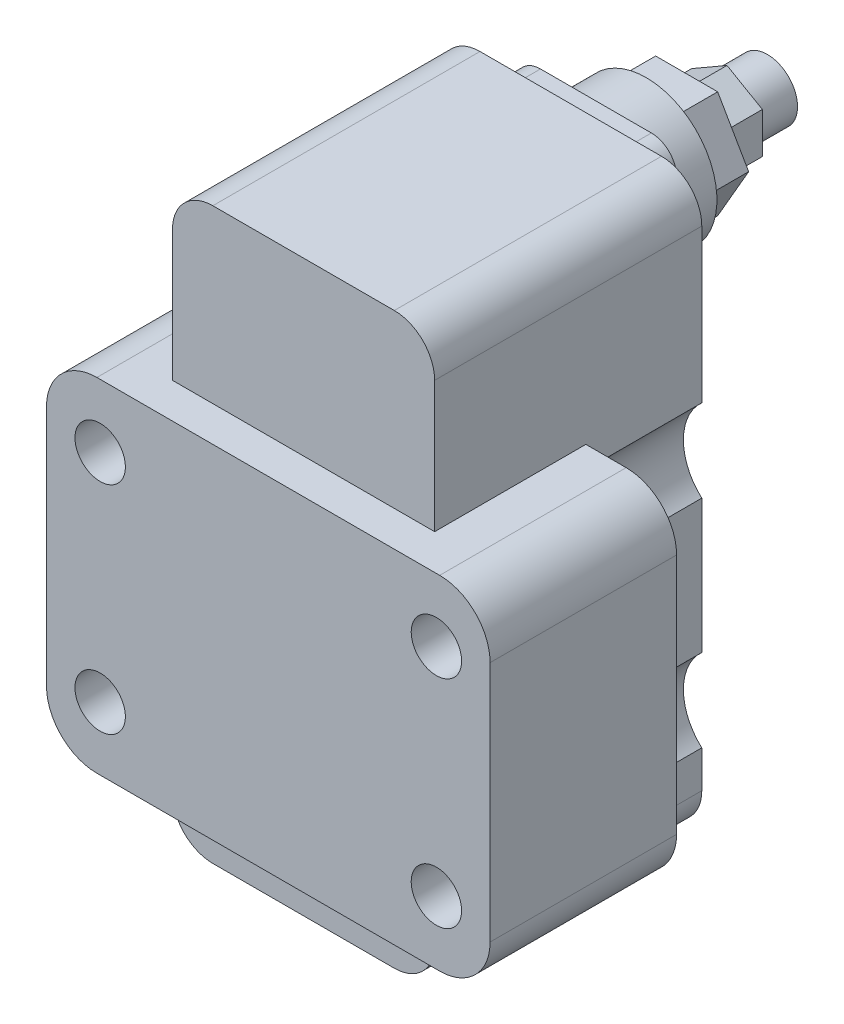
SolidWorks part; units mm, degrees
ref_plane "Front" through (0, 0, 0) normal (0, 0, 1) x (1, 0, 0)
ref_plane "Top" through (0, 0, 0) normal (0, 1, 0) x (1, 0, 0)
ref_plane "Right" through (0, 0, 0) normal (1, 0, 0) x (0, 0, -1)
sketch "草图1" plane through (0, 0, 0) normal (0, 0, 1) x (1, 0, 0)
  line L1 (-44, 34) -> (44, 34)
  line L2 (-44, 34) -> (-44, -34)
  line L3 (-44, -34) -> (44, -34)
  line L4 (44, 34) -> (44, -34)
  line L5 (-44, 34) -> (44, -34) construction
  line L6 (-44, -34) -> (44, 34) construction
  point P0 (0, 0)
  dimension "D1" = 68
  dimension "D2" = 88
extrude "凸台-拉伸1" add sketch "草图1" along normal blind 37
sketch "草图2" plane through (0, 0, 37) normal (0, 0, 1) x (1, 0, 0)
  line L1 (-44, -34) -> (44, -34) construction
  line L2 (-33.35, 21.45) -> (33.35, 21.45) construction
  line L3 (-33.35, 21.45) -> (-33.35, -21.45) construction
  line L4 (-33.35, -21.45) -> (33.35, -21.45) construction
  line L5 (33.35, 21.45) -> (33.35, -21.45) construction
  line L6 (-26, 68) -> (26, 68)
  line L7 (-26, 68) -> (-26, -45)
  line L8 (-26, -45) -> (26, -45)
  line L9 (26, 68) -> (26, -45)
  point P0 (0, 21.45)
  point P1 (-33.35, 0)
  point P11 (0, -45)
  dimension "D1" = 66.7
  dimension "D2" = 42.9
  dimension "D3" = 52
  dimension "D4" = 113
  dimension "D5" = 11
extrude "凸台-拉伸2" add sketch "草图2" against normal blind 60
sketch "草图3" plane through (0, 0, -23) normal (0, 0, -1) x (-1, 0, 0)
  circle A0 centre (-33.35, 21.45) radius 5
  circle A1 centre (33.35, 21.45) radius 5
  circle A2 centre (33.35, -21.45) radius 5
  circle A3 centre (-33.35, -21.45) radius 5
  dimension "D1" = 10
  dimension "D2" = 10
  dimension "D3" = 10
  dimension "D4" = 10
extrude "切除-拉伸1" cut sketch "草图3" against normal blind 60
sketch "草图4" plane through (0, 0, -23) normal (0, 0, -1) x (-1, 0, 0)
  line L1 (0, 26.1401) -> (0, -15.2183) construction
  line L2 (-12.4441, 0) -> (10.2481, 0) construction
  line L3 (-26, 68) -> (-26, -45) construction
  line L4 (-26, 45.3553) -> (26, 45.3553) construction
  line L5 (-26, 45.3553) -> (-26, -38.8255) construction
  line L6 (-26, -38.8255) -> (26, -38.8255) construction
  line L7 (26, 45.3553) -> (26, -38.8255) construction
  line L8 (26, 68) -> (26, -45) construction
  line L9 (-26, 29.634) -> (-26, 13.266)
  line L10 (26, 29.634) -> (26, 13.266)
  line L11 (26, -13.266) -> (26, -29.634)
  line L12 (-26, -13.266) -> (-26, -29.634)
  arc A0 (26, 29.634) -> (26, 13.266) centre (33.35, 21.45) ccw
  arc A1 (-26, 29.634) -> (-26, 13.266) centre (-33.35, 21.45) cw
  arc A2 (26, -29.634) -> (26, -13.266) centre (33.35, -21.45) cw
  arc A3 (-26, -29.634) -> (-26, -13.266) centre (-33.35, -21.45) ccw
  dimension "D1" = 22
extrude "切除-拉伸2" cut sketch "草图4" against normal up to surface (23 mm away) up to face at (-28.35, 21.45, 0)
sketch "草图5" plane through (0, 0, 0) normal (0, 0, -1) x (-1, 0, 0)
  line L1 (-34, 34) -> (34, 34)
  line L2 (-44, 24) -> (-44, -24)
  line L3 (-34, -34) -> (34, -34)
  line L4 (44, 24) -> (44, -24)
  arc A0 (-44, -24) -> (-34, -34) centre (-34, -24) ccw
  arc A1 (34, -34) -> (44, -24) centre (34, -24) ccw
  arc A2 (34, 34) -> (44, 24) centre (34, 24) cw
  arc A3 (-34, 34) -> (-44, 24) centre (-34, 24) ccw
  point P10 (44, -34)
  point P15 (-44, 34)
  dimension "D1" = 10
extrude "切除-拉伸3" cut sketch "草图5" against normal through all flip side to cut
sketch "草图7" plane through (0, 0, 0) normal (0, 0, 1) x (1, 0, 0)
  line L4 (-26, 68) -> (-26, 34)
  line L5 (-26, 34) -> (26, 34)
  line L6 (26, 34) -> (26, 68)
  line L7 (26, 68) -> (-26, 68)
  line L8 (-26, 68) -> (-26, 34)
  line L9 (-26, 34) -> (26, 34)
  line L10 (26, 34) -> (26, 68)
  line L11 (26, 68) -> (-26, 68)
  line L12 (26, -45) -> (26, -34)
  line L13 (26, -34) -> (-26, -34)
  line L14 (-26, -34) -> (-26, -45)
  line L15 (-26, -45) -> (26, -45)
  line L16 (26, -45) -> (26, -34)
  line L17 (26, -34) -> (-26, -34)
  line L18 (-26, -34) -> (-26, -45)
  line L19 (-26, -45) -> (26, -45)
  dimension "D1" = 0
  dimension "D2" = 0
extrude "凸台-拉伸3" add sketch "草图7" along normal blind 30
fillet "圆角1" radius 8 4 edges at (-26, 68, 3.5) (26, 68, 3.5) (-26, -45, 3.5) (26, -45, 3.5)
sketch "草图8" plane through (0, 0, -23) normal (0, 0, -1) x (-1, 0, 0)
  line L0 (-18, 68) -> (18, 68) construction
  line L1 (-16, 66) -> (16, 66)
  line L2 (-16, 66) -> (-16, 36)
  line L3 (-16, 36) -> (16, 36)
  line L4 (16, 66) -> (16, 36)
  point P4 (0, 68)
  point P7 (0, 66)
  point P10 (16, 51)
  dimension "D1" = 17
  dimension "D2" = 2
  dimension "D3" = 32
extrude "凸台-拉伸4" add sketch "草图8" along normal blind 5
sketch "草图9" plane through (0, 0, -28) normal (0, 0, -1) x (-1, 0, 0)
  line L0 (16, 66) -> (-16, 66) construction
  line L1 (12.2992, 51) -> (6.1496, 61.6514) construction
  line L2 (6.1496, 61.6514) -> (-6.1496, 61.6514) construction
  line L3 (-6.1496, 61.6514) -> (-12.2992, 51) construction
  line L4 (-12.2992, 51) -> (-6.1496, 40.3486) construction
  line L5 (-6.1496, 40.3486) -> (6.1496, 40.3486) construction
  line L6 (6.1496, 40.3486) -> (12.2992, 51) construction
  line L8 (-18, 68) -> (18, 68) construction
  circle A0 centre (0, 51) radius 10.6514 construction
  circle A1 centre (0, 51) radius 14
  dimension "D2" = 28
  dimension "D1" = 17
extrude "凸台-拉伸5" add sketch "草图9" along normal blind 10
sketch "草图10" plane through (0, 0, -38) normal (0, 0, -1) x (-1, 0, 0)
  line L0 (-6.1496, 61.6514) -> (-12.2992, 51) construction
  line L1 (-12.2992, 51) -> (-6.1496, 40.3486) construction
  line L2 (-6.1496, 40.3486) -> (6.1496, 40.3486) construction
  line L3 (6.1496, 40.3486) -> (12.2992, 51) construction
  line L4 (12.2992, 51) -> (6.1496, 61.6514) construction
  line L5 (6.1496, 61.6514) -> (-6.1496, 61.6514) construction
  line L6 (-6.1496, 61.6514) -> (-12.2992, 51)
  line L7 (-12.2992, 51) -> (-6.1496, 40.3486)
  line L8 (-6.1496, 40.3486) -> (6.1496, 40.3486)
  line L9 (6.1496, 40.3486) -> (12.2992, 51)
  line L10 (12.2992, 51) -> (6.1496, 61.6514)
  line L11 (6.1496, 61.6514) -> (-6.1496, 61.6514)
extrude "凸台-拉伸6" add sketch "草图10" along normal blind 8
fillet "圆角2" radius 5 4 edges at (16, 66, -25.5) (-16, 36, -25.5) (16, 36, -25.5) (-16, 66, -25.5)
sketch "草图11" plane through (0, 0, -46) normal (0, 0, -1) x (-1, 0, 0)
  line L1 (0, 42.8985) -> (7.0161, 46.9492)
  line L2 (7.0161, 46.9492) -> (7.0161, 55.0508)
  line L3 (7.0161, 55.0508) -> (0, 59.1015)
  line L4 (0, 59.1015) -> (-7.0161, 55.0508)
  line L5 (-7.0161, 55.0508) -> (-7.0161, 46.9492)
  line L6 (-7.0161, 46.9492) -> (0, 42.8985)
  circle A0 centre (0, 51) radius 7.0161 construction
extrude "凸台-拉伸7" add sketch "草图11" along normal blind 8
sketch "草图12" plane through (0, 0, -54) normal (0, 0, -1) x (-1, 0, 0)
  circle A0 centre (0, 51) radius 6
  dimension "D1" = 12
extrude "凸台-拉伸8" add sketch "草图12" along normal blind 8
